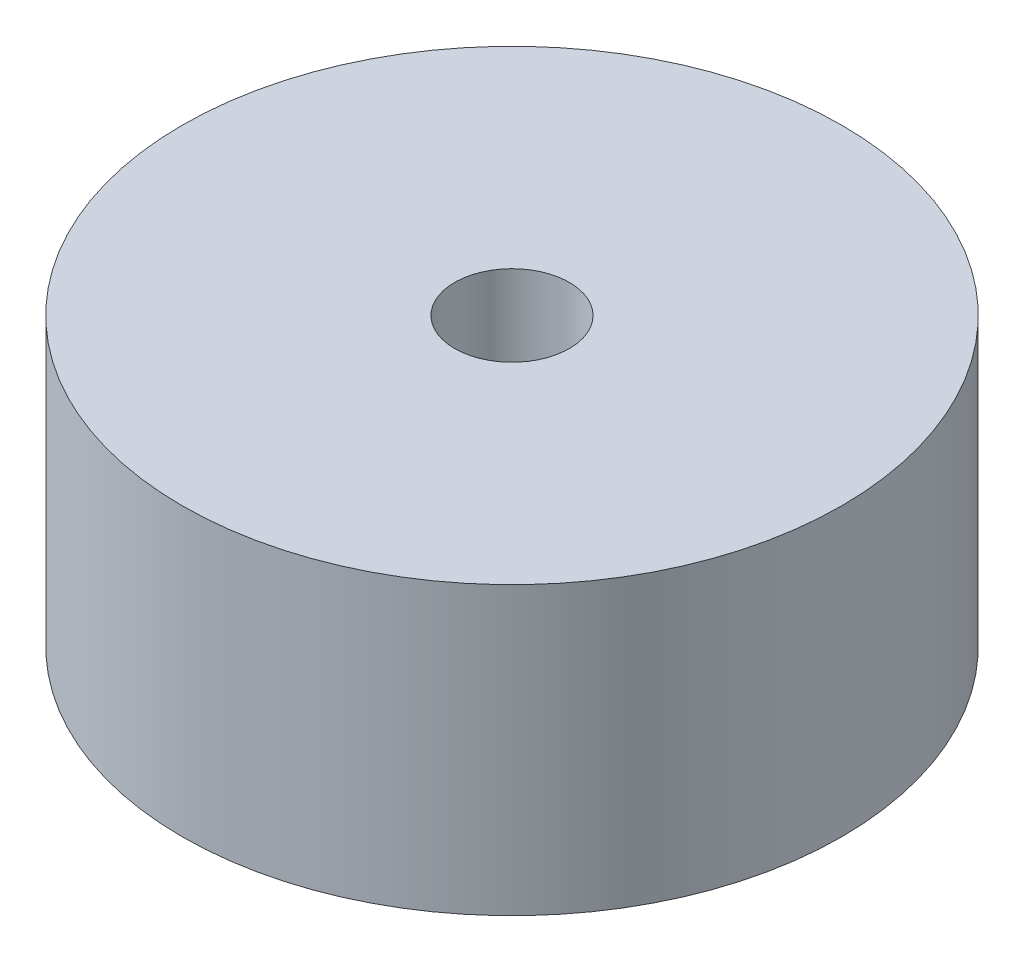
SolidWorks part; units mm, degrees
ref_plane "Front Plane" through (0, 0, 0) normal (0, 0, 1) x (1, 0, 0)
ref_plane "Top Plane" through (0, 0, 0) normal (0, 1, 0) x (1, 0, 0)
ref_plane "Right Plane" through (0, 0, 0) normal (1, 0, 0) x (0, 0, -1)
sketch "Sketch1" plane through (0, 0, 0) normal (0, 1, 0) x (1, 0, 0)
  circle A0 centre (0, 0) radius 23
  dimension "D1" = 46
extrude "Boss-Extrude1" add sketch "Sketch1" along normal blind 20
sketch "Sketch2" plane through (0, 20, 0) normal (0, 1, 0) x (1, 0, 0)
  circle A0 centre (0, 0) radius 4
  dimension "D1" = 8
extrude "Cut-Extrude1" cut sketch "Sketch2" against normal up to surface (20 mm away) up to face at (0, 0, 23)
hole_wizard "M3x0.5 Tapped Hole1" positions "Sketch3" profile "Sketch4" tap size "M3x0.5" standard "ANSI Metric"
sketch "Sketch3" plane through (0, 0, 0) normal (0, -1, 0) x (-1, 0, 0)
  line L0 (-6.7175, 6.7175) -> (6.7175, 6.7175) construction
  line L1 (6.7175, 6.7175) -> (6.7175, -6.7175) construction
  line L2 (6.7175, -6.7175) -> (-6.7175, -6.7175) construction
  line L3 (-6.7175, -6.7175) -> (-6.7175, 6.7175) construction
  circle A0 centre (0, 0) radius 9.5 construction
  circle A1 centre (0, 0) radius 7.5 construction
  point P35 (-7.5, 0)
  point P37 (7.5, 0)
  point P39 (0, 7.5)
  point P41 (0, -7.5)
  point P43 (-6.7175, 6.7175)
  point P45 (-6.7175, -6.7175)
  point P47 (6.7175, -6.7175)
  point P49 (6.7175, 6.7175)
  dimension "D1" = 19
  dimension "D2" = 15
sketch "Sketch4" plane through (-6.7175, 0, -6.7175) normal (1, 0, 0) x (0, 0, -1)
  line L0 (0, 0) -> (0, 7.2511)
  line L1 (0, 7.2511) -> (1.25, 6.5)
  line L2 (1.25, 6.5) -> (1.25, 0)
  line L5 (1.25, 0) -> (0, 0)
  line L10 (0, 7.2511) -> (-1.25, 6.5) construction
  line L11 (0, -6.35) -> (0, 107.95) construction
  dimension "Tap Drill Dia." = 2.5
  dimension "Tap Drill Depth" = 6.5
  dimension "Drill Angle" = 118
cosmetic thread "Hole Thread1" parameters "D1"=5, "D2"=3
cosmetic thread "Hole Thread2" parameters "D1"=5, "D2"=3
cosmetic thread "Hole Thread3" parameters "D1"=5, "D2"=3
cosmetic thread "Hole Thread4" parameters "D1"=5, "D2"=3
cosmetic thread "Hole Thread5" parameters "D1"=5, "D2"=3
cosmetic thread "Hole Thread6" parameters "D1"=5, "D2"=3
cosmetic thread "Hole Thread7" parameters "D1"=5, "D2"=3
cosmetic thread "Hole Thread8" parameters "D1"=5, "D2"=3
